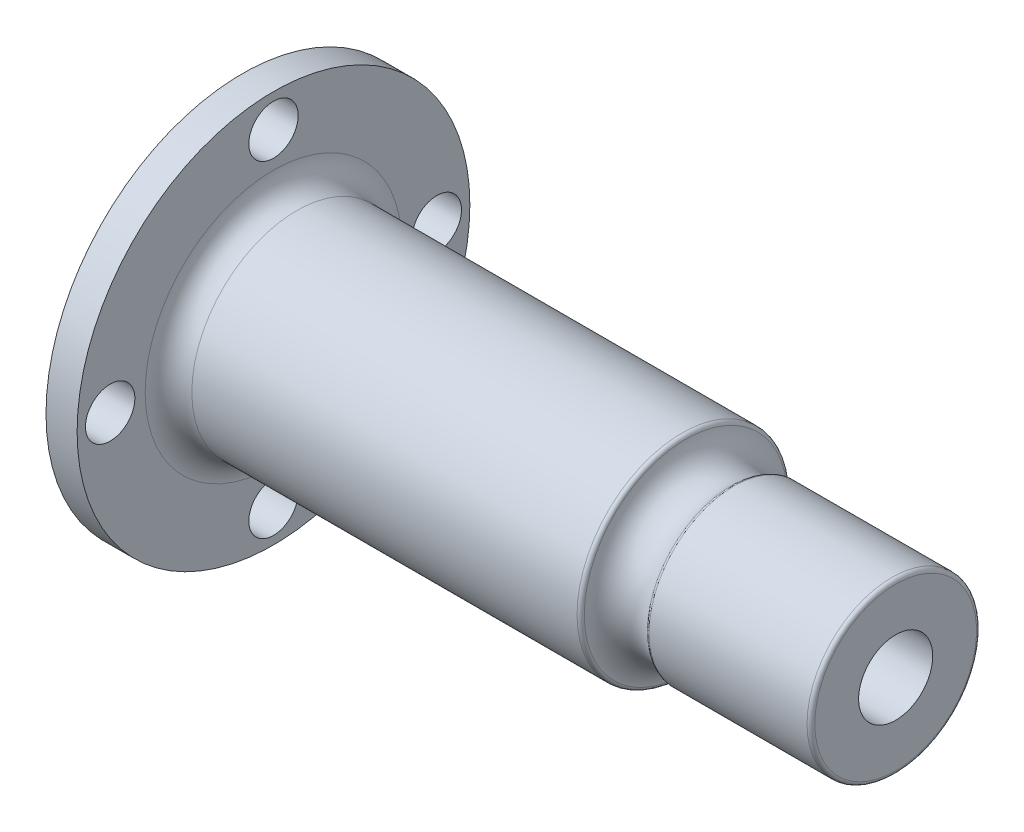
SolidWorks part; units mm, degrees
material "Plain Carbon Steel"
ref_plane "Front Plane" through (0, 0, 0) normal (0, 0, 1) x (1, 0, 0)
ref_plane "Top Plane" through (0, 0, 0) normal (0, 1, 0) x (1, 0, 0)
ref_plane "Right Plane" through (0, 0, 0) normal (1, 0, 0) x (0, 0, -1)
sketch "Sketch1" plane through (0, 0, 0) normal (0, 0, 1) x (1, 0, 0)
  line L0 (-159.7273, 0) -> (159.7273, 0) construction
  line L1 (134.6, 0) -> (134.6, 10.9)
  line L2 (134.6, 10.9) -> (113.6, 10.9)
  line L3 (107.6, 13.5) -> (54.6, 13.5)
  line L4 (54.6, 13.5) -> (54.6, 27.5)
  line L5 (54.6, 27.5) -> (47.6, 27.5)
  line L6 (47.6, 27.5) -> (47.6, 32.25)
  line L7 (47.6, 32.25) -> (44.6, 32.25)
  line L8 (44.6, 32.25) -> (44.6, 37)
  line L9 (44.6, 37) -> (40.6, 37)
  line L10 (40.6, 37) -> (40.6, 42)
  line L11 (40.6, 42) -> (23, 42)
  line L12 (23, 42) -> (23, 43)
  line L13 (23, 43) -> (5, 43)
  line L14 (5, 43) -> (5, 44)
  line L15 (5, 44) -> (0, 44)
  line L16 (0, 44) -> (0, 0)
  line L17 (0, 0) -> (134.6, 0)
  line L18 (107.6, 13.5) -> (107.6, 16.2865) construction
  arc A0 (107.6, 13.5) -> (113.6, 10.9) centre (111.1633, 13.5) ccw
  dimension "D1" = 21.8
  dimension "D2" = 21
  dimension "D3" = 6
  dimension "D4" = 53
  dimension "D5" = 27
  dimension "D6" = 55
  dimension "D7" = 64.5
  dimension "D8" = 74
  dimension "D9" = 84
  dimension "D10" = 86
  dimension "D11" = 88
  dimension "D12" = 7
  dimension "D13" = 3
  dimension "D14" = 4
  dimension "D15" = 17.6
  dimension "D16" = 18
  dimension "D17" = 5
revolve "Revolve1" add sketch "Sketch1"
fillet "Fillet1" radius 0.5 12 edges at (134.6, 0, 10.9) (113.6, 0, 10.9) (107.6, 0, 13.5) (54.6, 0, 27.5) (47.6, 0, 27.5) (47.6, 0, 32.25) (44.6, 0, 32.25) (44.6, 0, 37) (40.6, 0, 37) (40.6, 0, 42) (23, 0, 42) (5, 0, 43)
fillet "Fillet2" radius 3 1 edges at (54.6, 0, 13.5)
sketch "Sketch2" plane through (0, 0, 0) normal (0, 0, 1) x (1, 0, 0)
  line L0 (-12.9368, 0) -> (142.522, 0) construction
  line L1 (39.6, 0) -> (43.0851, 8) construction
  line L2 (50.6, 25.25) -> (64.0026, 25.25)
  line L3 (64.0026, 25.25) -> (64.0026, 54.4464)
  line L4 (64.0026, 54.4464) -> (-9.3548, 54.4464)
  line L5 (-9.3548, 54.4464) -> (-9.3548, 0)
  line L6 (-9.3548, 0) -> (39.6, 0)
  line L8 (54.6, -27) -> (54.6, 27) construction
  line L9 (43.0851, 8) -> (43.0851, 0)
  line L10 (43.0851, 0) -> (39.6, 0)
  line L11 (43.0851, 8) -> (50.6, 25.25)
  dimension "D1" = 4
  dimension "D2" = 50.5
  dimension "D3" = 15
  dimension "D4" = 16
revolve "Cut-Revolve1" cut sketch "Sketch2" angle 360 about L0
sketch "Sketch3" plane through (134.6, 0, 0) normal (1, 0, 0) x (0, 0, -1)
  circle A0 centre (0, 0) radius 4.7625
  dimension "D1" = 9.525
extrude "Cut-Extrude1" cut sketch "Sketch3" against normal through all
sketch "Sketch4" plane through (0, 0, 0) normal (1, 0, 0) x (0, 0, -1)
  line L0 (0, 0) -> (0, 21) construction
  circle A0 centre (21, 0) radius 3.175
  circle A1 centre (0, -21) radius 3.175
  circle A2 centre (0, 21) radius 3.175
  circle A3 centre (-21, 0) radius 3.175
  point P13 (0, 0)
  dimension "D1" = 21
  dimension "D2" = 6.35
  dimension "D3" = 4
extrude "Cut-Extrude3" cut sketch "Sketch4" along normal through all
